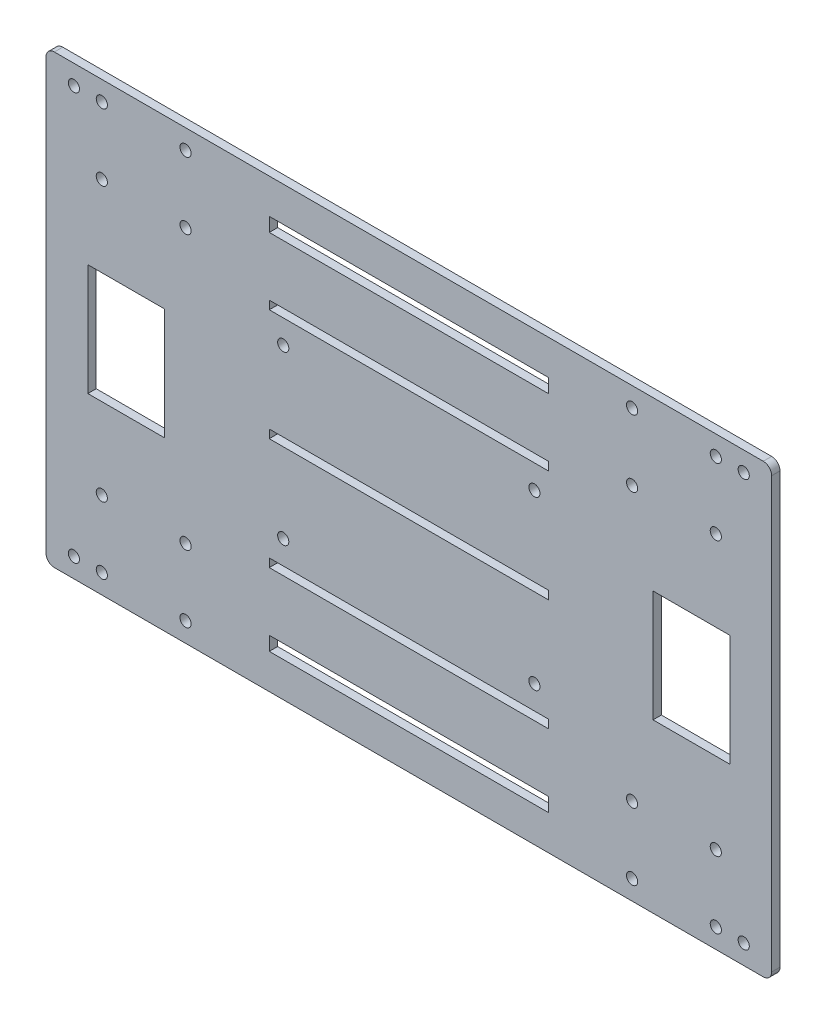
SolidWorks part; units mm, degrees
ref_plane "前视基准面" through (0, 0, 0) normal (0, 0, 1) x (1, 0, 0)
ref_plane "上视基准面" through (0, 0, 0) normal (0, 1, 0) x (1, 0, 0)
ref_plane "右视基准面" through (0, 0, 0) normal (1, 0, 0) x (0, 0, -1)
sketch "Model" plane through (0, 0, 0) normal (0, 0, 1) x (1, 0, 0)
  line L0 (-87.5, -20) -> (-87.5, 20)
  line L1 (-115, -20) -> (-87.5, -20)
  line L2 (-115, 20) -> (-115, -20)
  line L3 (-87.5, 20) -> (-115, 20)
  line L4 (87.5, -20) -> (115, -20)
  line L5 (87.5, 20) -> (87.5, -20)
  line L6 (115, 20) -> (87.5, 20)
  line L7 (115, -20) -> (115, 20)
  line L8 (-50, -62.5) -> (-50, -67.5)
  line L9 (50, -62.5) -> (-50, -62.5)
  line L10 (50, -67.5) -> (50, -62.5)
  line L11 (-50, -67.5) -> (50, -67.5)
  line L12 (50, 62.5) -> (50, 67.5)
  line L13 (-50, 62.5) -> (50, 62.5)
  line L14 (-50, 67.5) -> (-50, 62.5)
  line L15 (50, 67.5) -> (-50, 67.5)
  line L16 (50, -1.5) -> (50, 1.5)
  line L17 (-50, -1.5) -> (50, -1.5)
  line L18 (-50, 1.5) -> (-50, -1.5)
  line L19 (50, 1.5) -> (-50, 1.5)
  line L20 (-50, -38.5) -> (-50, -41.5)
  line L21 (50, -38.5) -> (-50, -38.5)
  line L22 (50, -41.5) -> (50, -38.5)
  line L23 (-50, -41.5) -> (50, -41.5)
  line L24 (50, 38.5) -> (50, 41.5)
  line L25 (-50, 38.5) -> (50, 38.5)
  line L26 (-50, 41.5) -> (-50, 38.5)
  line L27 (50, 41.5) -> (-50, 41.5)
  line L28 (130, -77) -> (130, 77)
  line L29 (127, 80) -> (-127, 80)
  line L30 (-130, 77) -> (-130, -77)
  line L31 (-127, -80) -> (127, -80)
  circle A0 centre (-110, 49) radius 2
  circle A1 centre (-80, 73) radius 2
  circle A2 centre (110, 73) radius 2
  circle A3 centre (-120, 73) radius 2
  circle A4 centre (80, 73) radius 2
  circle A5 centre (110, 49) radius 2
  circle A6 centre (80, -49) radius 2
  circle A7 centre (110, -73) radius 2
  circle A8 centre (-80, -73) radius 2
  circle A9 centre (-110, -49) radius 2
  arc A10 (130, 77) -> (127, 80) centre (127, 77) ccw
  arc A11 (-127, 80) -> (-130, 77) centre (-127, 77) ccw
  arc A12 (-130, -77) -> (-127, -80) centre (-127, -77) ccw
  arc A13 (127, -80) -> (130, -77) centre (127, -77) ccw
  circle A14 centre (-80, -49) radius 2
  circle A15 centre (-110, -73) radius 2
  circle A16 centre (80, -73) radius 2
  circle A17 centre (110, -49) radius 2
  circle A18 centre (80, 49) radius 2
  circle A19 centre (120, 73) radius 2
  circle A20 centre (120, -73) radius 2
  circle A21 centre (-110, 73) radius 2
  circle A22 centre (-80, 49) radius 2
  circle A23 centre (-120, -73) radius 2
extrude "凸台-拉伸1" add sketch "Model" along normal blind 3
sketch "草图2" plane through (0, 0, 3) normal (0, 0, 1) x (1, 0, 0)
  line L0 (-50, -35) -> (-45, -35)
  line L1 (-50, -35) -> (50, -35)
  line L2 (-50, -35) -> (-50, 35)
  line L3 (-50, 35) -> (50, 35)
  line L4 (50, -35) -> (50, 35)
  line L5 (-50, -35) -> (50, 35) construction
  line L6 (-50, 35) -> (50, -35) construction
  line L7 (-45, -35) -> (-45, -30)
  line L8 (0, 0) -> (15.8068, 0)
  line L9 (0, 0) -> (0, 11.9671)
  circle A0 centre (-45, -30) radius 2
  circle A1 centre (-45, 30) radius 2
  circle A2 centre (45, -30) radius 2
  circle A3 centre (45, 30) radius 2
  point P0 (0, 0)
  dimension "D5" = 4
  dimension "D1" = 70
  dimension "D2" = 100
  dimension "D3" = 5
  dimension "D4" = 5
extrude "切除-拉伸1" cut sketch "草图2" against normal blind 10 contours A1 | A3 | A2 | A0
